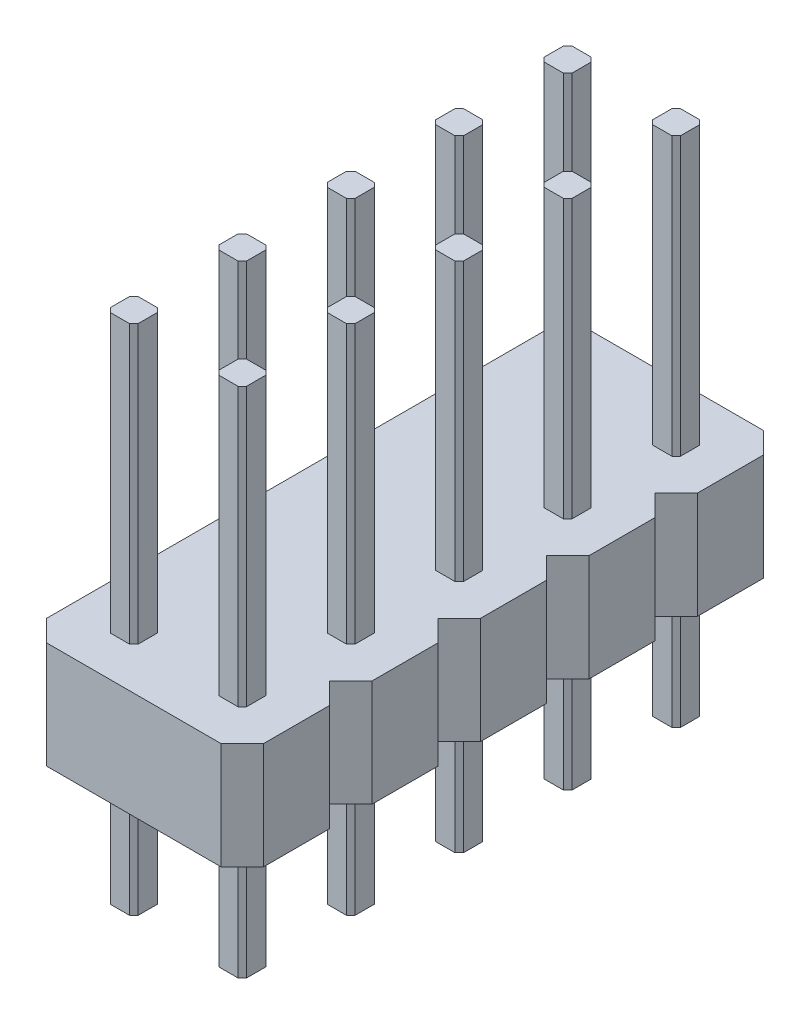
SolidWorks part; units mm, degrees
ref_plane "Front Plane" through (0, 0, 0) normal (0, 0, 1) x (1, 0, 0)
ref_plane "Top Plane" through (0, 0, 0) normal (0, 1, 0) x (1, 0, 0)
ref_plane "Right Plane" through (0, 0, 0) normal (1, 0, 0) x (0, 0, -1)
sketch "Sketch1" plane through (0, 0, 0) normal (0, 1, 0) x (1, 0, 0)
  line L0 (-0.225, -0.325) -> (-0.325, -0.225)
  line L1 (0.225, -0.325) -> (-0.225, -0.325)
  line L2 (0.325, -0.225) -> (0.325, 0.225)
  line L3 (0.225, 0.325) -> (-0.225, 0.325)
  line L4 (-0.325, -0.225) -> (-0.325, 0.225)
  line L5 (0.325, -0.325) -> (-0.325, 0.325) construction
  line L6 (0.325, 0.325) -> (-0.325, -0.325) construction
  line L7 (-0.225, 0.325) -> (-0.325, 0.225)
  line L8 (0.325, 0.225) -> (0.225, 0.325)
  line L9 (0.325, -0.225) -> (0.225, -0.325)
  point P0 (0, 0)
  dimension "D1" = 0.65
extrude "Boss-Extrude1" add sketch "Sketch1" along normal blind 12
pattern_linear "LPattern2" count 2 spacing 2.54 along (1, 0, 0) of bodies 101
ref_plane "Plane1" through (0, 3, 0) normal (0, -1, 0) x (-1, 0, 0)
sketch "Sketch2" plane through (0, 3, 0) normal (0, -1, 0) x (-1, 0, 0)
  line L0 (0.325, 0) -> (-2.865, 0) construction
  line L1 (0.325, 0.225) -> (0.325, -0.225) construction
  line L2 (-2.865, -0.225) -> (-2.865, 0.225) construction
  line L3 (-3.31, 1.27) -> (-3.81, 0.77)
  line L4 (0.77, -1.27) -> (-3.31, -1.27)
  line L5 (1.27, -0.77) -> (1.27, 0.77)
  line L6 (0.77, 1.27) -> (-3.31, 1.27)
  line L7 (-3.81, -0.77) -> (-3.81, 0.77)
  line L8 (1.27, -1.27) -> (-3.81, 1.27) construction
  line L9 (1.27, 1.27) -> (-3.81, -1.27) construction
  line L10 (-3.31, -1.27) -> (-3.81, -0.77)
  line L11 (1.27, -0.77) -> (0.77, -1.27)
  line L12 (1.27, 0.77) -> (0.77, 1.27)
  point P6 (-1.27, 0)
  dimension "D1" = 5.08
  dimension "D2" = 2.54
extrude "Boss-Extrude2" add sketch "Sketch2" against normal blind 2.5
pattern_linear "LPattern3" count 5 spacing 2.54 along (0, 0, 1) of bodies 104
combine bodies "Combine1" operation type add bodies to combine 104 105 106 107 108
